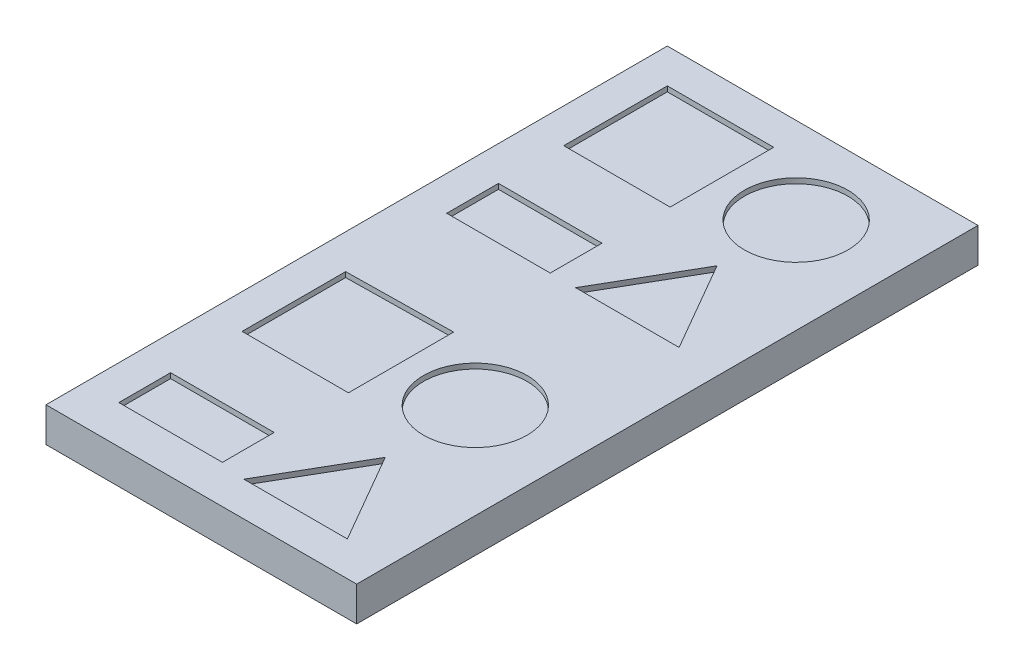
SolidWorks part; units mm, degrees
ref_plane "Front Plane" through (0, 0, 0) normal (0, 0, 1) x (1, 0, 0)
ref_plane "Top Plane" through (0, 0, 0) normal (0, 1, 0) x (1, 0, 0)
ref_plane "Right Plane" through (0, 0, 0) normal (1, 0, 0) x (0, 0, -1)
sketch "Sketch1" plane through (0, 0, 0) normal (0, 1, 0) x (1, 0, 0)
  line L1 (-90, 180) -> (90, 180)
  line L2 (-90, 180) -> (-90, -180)
  line L3 (-90, -180) -> (90, -180)
  line L4 (90, 180) -> (90, -180)
  line L5 (-90, 180) -> (90, -180) construction
  line L6 (-90, -180) -> (90, 180) construction
  point P0 (0, 0)
  dimension "D1" = 180
  dimension "D2" = 360
extrude "Boss-Extrude1" add sketch "Sketch1" against normal blind 20
sketch "Sketch2" plane through (0, 0, 0) normal (0, 1, 0) x (1, 0, 0)
  line L0 (90, 180) -> (-90, 180) construction
  line L1 (-70, 160) -> (64.6562, 160) construction
  line L2 (-70, 160) -> (-70, -157.8014) construction
  line L3 (-70, -157.8014) -> (64.6562, -160.0401) construction
  line L4 (64.6562, 160) -> (64.6562, -160.0401) construction
  line L7 (90, -180) -> (90, 180) construction
  line L8 (-70, 32.1622) -> (-10, 32.1622)
  line L9 (-70, 32.1622) -> (-70, 62.1622)
  line L10 (-70, 160) -> (-8.3753, 160)
  line L11 (-70, 160) -> (-70, 100)
  line L12 (-70, 100) -> (-8.3753, 100)
  line L13 (-8.3753, 160) -> (-8.3753, 100)
  line L14 (4.6562, 32.1622) -> (64.6562, 32.1622)
  line L15 (64.6562, 32.1622) -> (34.6562, 84.1237)
  line L16 (34.6562, 84.1237) -> (4.6562, 32.1622)
  line L17 (-70, 62.1622) -> (-10, 62.1622)
  line L18 (-10, 32.1622) -> (-10, 62.1622)
  line L19 (4.6562, -160.0401) -> (64.6562, -160.0401)
  line L20 (-70, -157.8014) -> (-10, -157.8014)
  line L21 (64.6562, -160.0401) -> (34.6562, -108.0786)
  line L22 (34.6562, -108.0786) -> (4.6562, -160.0401)
  line L23 (-10, -157.8014) -> (-10, -127.8014)
  line L24 (-8.3753, -25.4415) -> (-8.3753, -86.3874)
  line L25 (-70, -24.258) -> (-70, -344.258) construction
  line L26 (-70, -26.3874) -> (-8.3753, -25.4415)
  line L27 (-70, -26.3874) -> (-70, -86.3874)
  line L28 (-70, -157.8014) -> (-70, -127.8014)
  line L29 (-70, -86.3874) -> (-8.3753, -86.3874)
  line L30 (-70, -24.258) -> (62.5564, -24.258) construction
  line L31 (-70, -127.8014) -> (-10, -127.8014)
  line L33 (-90, 180) -> (-90, -180) construction
  circle A0 centre (34.6562, 130) radius 30
  circle A1 centre (34.6562, -55.9145) radius 30
  point P0 (0, 0)
  point P5 (-1.0617, -186.4566)
  point P29 (4.6562, 130)
  point P37 (0, 0)
  point P43 (0, 0)
  point P48 (-8.3753, -55.9145)
  point P49 (34.6562, 100)
  dimension "D4" = 60
  dimension "D8" = 60
  dimension "D9" = 60
  dimension "D1" = 20
  dimension "D2" = 60
  dimension "D3" = 60
  dimension "D5" = 60
  dimension "D6" = 60
  dimension "D7" = 30
  dimension "D10" = 60
  dimension "D11" = 30
  dimension "D12" = 20
extrude "Cut-Extrude1" cut sketch "Sketch2" against normal blind 3
